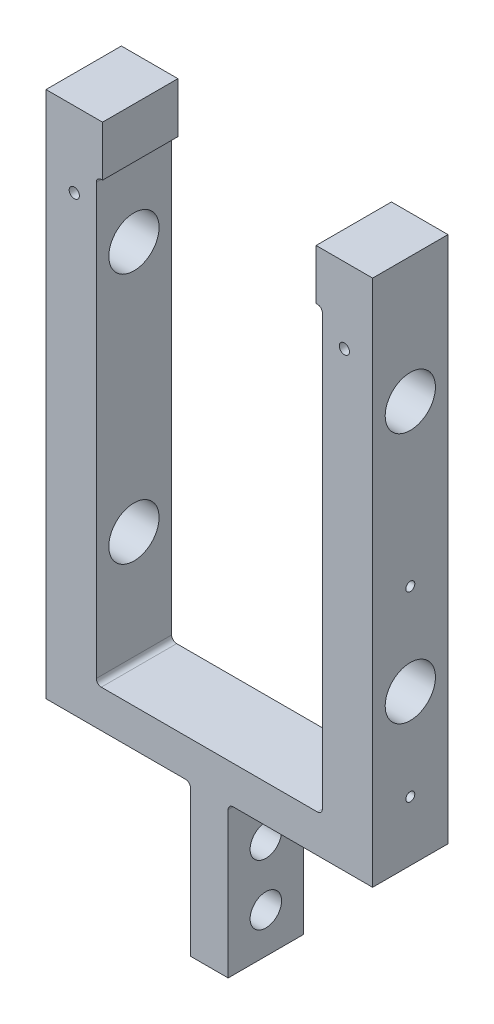
SolidWorks part; units mm, degrees
material "6061 Alloy"
ref_plane "Front Plane" through (0, 0, 0) normal (0, 0, 1) x (1, 0, 0)
ref_plane "Top Plane" through (0, 0, 0) normal (0, 1, 0) x (1, 0, 0)
ref_plane "Right Plane" through (0, 0, 0) normal (1, 0, 0) x (0, 0, -1)
sketch "Sketch1" plane through (0, 0, 0) normal (0, 0, 1) x (1, 0, 0)
  line L7 (9.525, 0) -> (-9.525, 0)
  line L13 (-9.525, 0) -> (-9.525, 19.05)
  line L14 (-9.525, 19.05) -> (-41.275, 19.05)
  line L15 (-41.275, 19.05) -> (-41.275, 131.5967)
  line L17 (-28.575, 139.7) -> (-28.575, 28.575)
  line L18 (-28.575, 28.575) -> (28.575, 28.575)
  line L19 (0, 29.8154) -> (0, -13.1535) construction
  line L20 (28.575, 139.7) -> (28.575, 28.575)
  line L22 (41.275, 19.05) -> (41.275, 131.5967)
  line L23 (9.525, 19.05) -> (41.275, 19.05)
  line L24 (9.525, 0) -> (9.525, 19.05)
  line L25 (41.275, 131.5967) -> (41.275, 152.4)
  line L26 (41.275, 152.4) -> (-41.275, 152.4)
  line L27 (-41.275, 152.4) -> (-41.275, 131.5967)
  line L29 (28.575, 139.7) -> (-28.575, 139.7)
  point P12 (0, 28.575)
  point P17 (0, 0)
  dimension "D1" = 19.05
  dimension "D2" = 57.15
  dimension "D3" = 19.05
  dimension "D4" = 82.55
  dimension "D5" = 111.125
  dimension "D6" = 12.7
  dimension "D7" = 152.4
extrude "Boss-Extrude1" add sketch "Sketch1" along normal mid plane 19.05
sketch "Sketch2" plane through (-41.275, 0, 0) normal (-1, 0, 0) x (0, 0, 1)
  line L0 (-26.0251, 0) -> (40.3307, 0) construction
  line L1 (0, 127) -> (0, 0) construction
  circle A0 centre (0, 57.15) radius 6.35
  circle A1 centre (0, 120.65) radius 6.35
  dimension "D2" = 12.7
  dimension "D1" = 12.7
  dimension "D4" = 63.5
  dimension "D3" = 57.15
extrude "Cut-Extrude1" cut sketch "Sketch2" against normal through all
sketch "Sketch4" plane through (0, 0, -9.525) normal (0, 0, -1) x (-1, 0, 0)
  line L1 (9.525, 0) -> (-9.525, 0) construction
  line L2 (9.525, 0) -> (9.525, 19.05) construction
  line L3 (9.525, 19.05) -> (-9.525, 19.05) construction
  line L4 (-9.525, 0) -> (-9.525, 19.05) construction
  line L5 (-4.7625, 19.0579) -> (4.7625, 19.0579) construction
  line L6 (-4.7625, 19.0579) -> (-4.7625, 0) construction
  line L7 (-4.7625, 0) -> (4.7625, 0) construction
  line L8 (4.7625, 19.0579) -> (4.7625, 0) construction
  line L9 (-4.7625, 19.0579) -> (4.7625, 0) construction
  line L10 (-4.7625, 0) -> (4.7625, 19.0579) construction
  line L11 (-9.525, 19.05) -> (-4.7625, 19.05)
  line L12 (-9.525, 19.05) -> (-9.525, 0)
  line L13 (-9.525, 0) -> (-4.7625, 0)
  line L14 (-4.7625, 19.05) -> (-4.7625, 0)
  line L15 (4.7625, 19.0579) -> (9.525, 19.0579)
  line L16 (4.7625, 19.0579) -> (4.7625, 0)
  line L17 (4.7625, 0) -> (9.525, 0)
  line L18 (9.525, 19.0579) -> (9.525, 0)
  point P6 (0, 9.529)
  dimension "D1" = 9.525
extrude "Cut-Extrude2" cut sketch "Sketch4" against normal through all
sketch "Sketch5" plane through (-4.7625, 0, 0) normal (-1, 0, 0) x (0, 0, 1)
  circle A0 centre (0, 6.35) radius 4.7625
  dimension "D1" = 9.525
  dimension "D2" = 6.35
sketch "Sketch6" plane through (41.275, 0, 0) normal (-1, 0, 0) x (0, 0, 1)
  line L0 (0, 80.1624) -> (0, 34.1376) construction
  point P5 (0, 57.15)
  dimension "D1" = 46.0248
hole_wizard "#4-40 Tapped Hole2" positions "Sketch12" profile "Sketch13" tap size "#4-40" standard "ANSI Inch"
sketch "Sketch12" plane through (41.275, 0, 0) normal (1, 0, 0) x (0, 0, -1)
  point P0 (0, 80.1624)
  point P3 (0, 34.1376)
sketch "Sketch13" plane through (41.275, 80.1624, 0) normal (0, 1, 0) x (0, 0, -1)
  line L0 (0, 0) -> (0, 13.3792)
  line L1 (0, 13.3792) -> (1.1303, 12.7)
  line L2 (1.1303, 12.7) -> (1.1303, 0)
  line L5 (1.1303, 0) -> (0, 0)
  line L10 (0, 13.3792) -> (-1.1303, 12.7) construction
  line L11 (0, -6.35) -> (0, 107.95) construction
  dimension "Tap Drill Dia." = 2.2606
  dimension "Tap Drill Depth" = 12.7
  dimension "Drill Angle" = 118
cosmetic thread "Hole Thread5" parameters "D1"=82.55, "D2"=2.8448
cosmetic thread "Hole Thread6" parameters "D1"=82.55, "D2"=2.8448
sketch "Sketch14" plane through (0, 0, 0) normal (0, -1, 0) x (1, 0, 0)
  line L1 (4.7625, -9.525) -> (-4.7625, -9.525)
  line L2 (4.7625, -9.525) -> (4.7625, 9.525)
  line L3 (4.7625, 9.525) -> (-4.7625, 9.525)
  line L4 (-4.7625, -9.525) -> (-4.7625, 9.525)
extrude "Boss-Extrude2" add sketch "Sketch14" along normal blind 19.05
hole_wizard "Hole1" positions "Sketch15" profile "Sketch16" legacy end condition through all
sketch "Sketch15" plane through (-4.7625, 0, 0) normal (-1, 0, 0) x (0, 0, 1)
  point P0 (0, 6.35)
  point P3 (0, -8.89)
  dimension "D1" = 8.89
sketch "Sketch16" plane through (-4.7625, 6.35, 0) normal (0, 1, 0) x (0, 0, 1)
  line L0 (0, 0) -> (0, 48.4245)
  line L1 (0, 48.4245) -> (3.9726, 46.0375)
  line L2 (3.9726, 46.0375) -> (3.9726, 0)
  line L4 (3.9726, 0) -> (0, 0)
  line L6 (0, 48.4245) -> (-3.9726, 46.0375) construction
  line L7 (0, -4.2442) -> (0, 117.3081) construction
  dimension "Diameter" = 7.9451
  dimension "Depth" = 46.0375
  dimension "Drill Angle" = 118
fillet "Fillet1" radius 1.27 6 edges at (4.7625, 19.05, 0) (-4.7625, 19.0579, 0) (-28.575, 28.575, 0) (28.575, 28.575, 0) (28.575, 139.7, 0) (-28.575, 139.7, 0)
sketch "Sketch17" plane through (0, 0, 9.525) normal (0, 0, 1) x (1, 0, 0)
  line L0 (0, 152.4) -> (0, 117.2896) construction
  line L1 (41.275, 152.4) -> (-41.275, 152.4) construction
  line L2 (23.5336, 152.4) -> (23.5336, 139.7) construction
  line L3 (27.305, 139.7) -> (-27.305, 139.7) construction
  line L4 (23.5336, 146.05) -> (-38.274, 146.05) construction
  line L6 (-26.9875, 152.4) -> (26.9875, 152.4)
  line L7 (-26.9875, 152.4) -> (-26.9875, 139.7)
  line L8 (-26.9875, 139.7) -> (26.9875, 139.7)
  line L9 (26.9875, 152.4) -> (26.9875, 139.7)
  line L10 (-26.9875, 152.4) -> (26.9875, 139.7) construction
  line L11 (-26.9875, 139.7) -> (26.9875, 152.4) construction
  point P11 (0, 146.05)
  point P12 (0, 146.05)
  dimension "D1" = 53.975
extrude "Cut-Extrude3" cut sketch "Sketch17" against normal through all
hole_wizard "#5-40 Tapped Hole1" positions "Sketch18" profile "Sketch19" tap size "#5-40" standard "ANSI Inch" end condition through all
sketch "Sketch18" plane through (0, 0, 9.525) normal (0, 0, -1) x (-1, 0, 0)
  line L0 (-34.1313, 152.4) -> (-34.1313, 117.2912) construction
  line L1 (-41.275, 152.4) -> (-26.9875, 152.4) construction
  line L3 (34.1313, 152.4) -> (34.1313, 122.5386) construction
  line L4 (26.9875, 152.4) -> (41.275, 152.4) construction
  point P0 (-34.1313, 133.35)
  point P2 (34.1313, 133.35)
  dimension "D1" = 19.05
sketch "Sketch19" plane through (34.1313, 133.35, 9.525) normal (1, 0, 0) x (0, -1, 0)
  line L0 (0, 0) -> (0, 19.05)
  line L1 (0, 19.05) -> (1.289, 19.05)
  line L2 (1.289, 19.05) -> (1.289, 0)
  line L5 (1.289, 0) -> (0, 0)
  line L11 (0, -6.35) -> (0, 107.95) construction
  dimension "Thru Tap Drill Dia." = 2.5781
  dimension "Thru Tap Drill Depth" = 19.05
cosmetic thread "Hole Thread9" parameters "D2"=3.175
cosmetic thread "Hole Thread10" parameters "D2"=3.175
equation "\"BoomDistance\"=2.5"
equation "\"D4@Sketch2\"=\"BoomDistance\""
